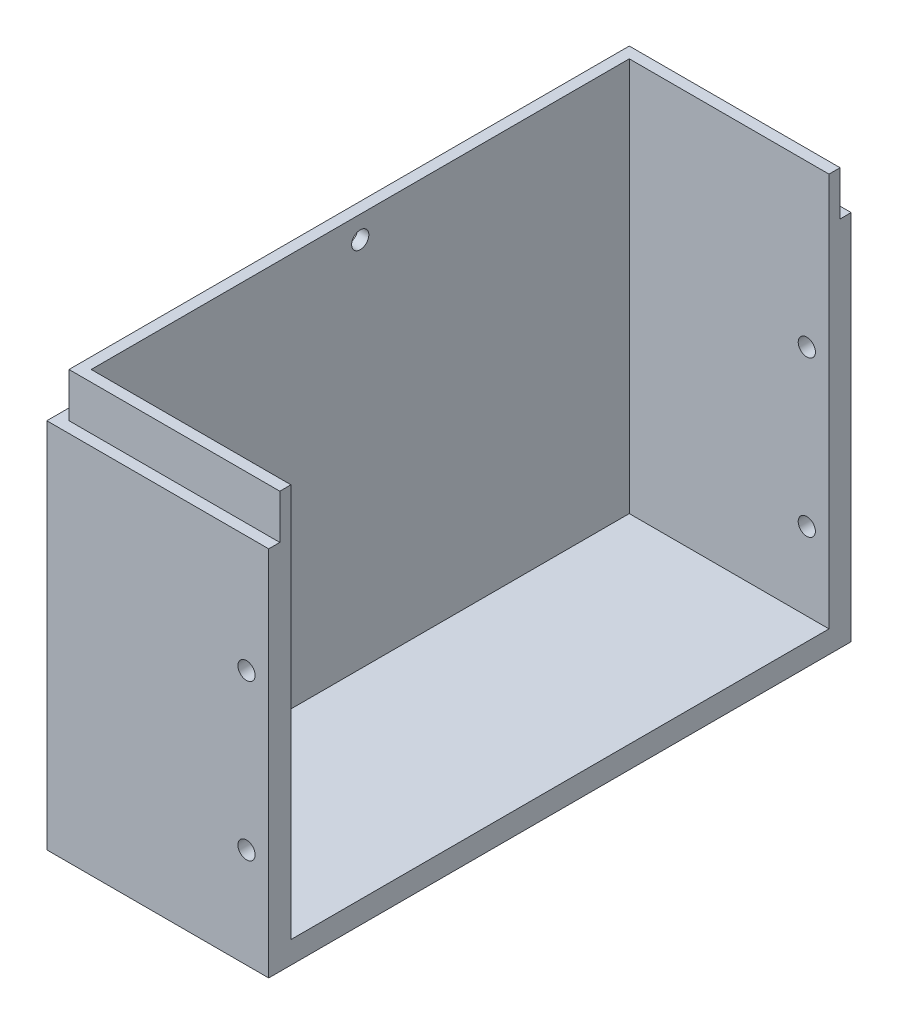
SolidWorks part; units mm, degrees
ref_plane "Front Plane" through (0, 0, 0) normal (0, 0, 1) x (1, 0, 0)
ref_plane "Top Plane" through (0, 0, 0) normal (0, 1, 0) x (1, 0, 0)
ref_plane "Right Plane" through (0, 0, 0) normal (1, 0, 0) x (0, 0, -1)
sketch "Sketch1" plane through (0, 0, 0) normal (0, 1, 0) x (1, 0, 0)
  line L1 (-20, 52.5) -> (20, 52.5)
  line L2 (-20, 52.5) -> (-20, -52.5)
  line L3 (-20, -52.5) -> (20, -52.5)
  line L4 (20, 52.5) -> (20, -52.5)
  line L5 (-20, 52.5) -> (20, -52.5) construction
  line L6 (-20, -52.5) -> (20, 52.5) construction
  point P0 (0, 0)
  dimension "D1" = 105
  dimension "D2" = 40
extrude "Boss-Extrude3" add sketch "Sketch1" along normal blind 75
sketch "Sketch4" plane through (20, 0, 0) normal (1, 0, 0) x (0, 0, -1)
  line L0 (-52.5, 75) -> (52.5, 75) construction
  line L1 (-48.5, 75) -> (48.5, 75)
  line L2 (-48.5, 75) -> (-48.5, 4)
  line L3 (-48.5, 4) -> (48.5, 4)
  line L4 (48.5, 75) -> (48.5, 4)
  line L5 (-52.5, 75) -> (-52.5, 0) construction
  line L6 (-52.5, 0) -> (52.5, 0) construction
  line L7 (52.5, 75) -> (52.5, 0) construction
  dimension "D1" = 4
  dimension "D2" = 4
  dimension "D3" = 4
extrude "Cut-Extrude2" cut sketch "Sketch4" against normal blind 36
sketch "Sketch5" plane through (0, 0, 52.5) normal (0, 0, 1) x (1, 0, 0)
  line L0 (-20, 75) -> (-20, 0) construction
  line L1 (20, 75) -> (-20, 75)
  line L2 (20, 75) -> (20, 67)
  line L3 (20, 67) -> (-20, 67)
  line L4 (-20, 75) -> (-20, 67)
  dimension "D1" = 8
extrude "Cut-Extrude3" cut sketch "Sketch5" against normal blind 2
sketch "Sketch6" plane through (0, 0, -52.5) normal (0, 0, -1) x (-1, 0, 0)
  line L0 (20, 75) -> (20, 0) construction
  line L1 (-20, 75) -> (20, 75)
  line L2 (-20, 75) -> (-20, 67)
  line L3 (-20, 67) -> (20, 67)
  line L4 (20, 75) -> (20, 67)
  dimension "D1" = 8
extrude "Cut-Extrude4" cut sketch "Sketch6" against normal blind 2
sketch "Sketch7" plane through (-20, 0, 0) normal (-1, 0, 0) x (0, 0, 1)
  line L1 (-50.5, 75) -> (50.5, 75)
  line L2 (-50.5, 75) -> (-50.5, 67)
  line L3 (-50.5, 67) -> (50.5, 67)
  line L4 (50.5, 75) -> (50.5, 67)
extrude "Cut-Extrude5" cut sketch "Sketch7" against normal blind 2
sketch "Sketch8" plane through (0, 0, 48.5) normal (0, 0, -1) x (-1, 0, 0)
  line L0 (-20, 75) -> (-20, 4) construction
  line L1 (16, 4) -> (-20, 4) construction
  circle A0 centre (-16, 18) radius 1.55
  circle A1 centre (-16, 46) radius 1.55
  dimension "D1" = 3.1
  dimension "D2" = 3.1
  dimension "D5" = 14
  dimension "D6" = 28
  dimension "D3" = 4
  dimension "D4" = 4
extrude "Cut-Extrude6" cut sketch "Sketch8" against normal through all and the other way through all
sketch "Sketch10" plane through (-18, 0, 0) normal (-1, 0, 0) x (0, 0, 1)
  line L0 (50.5, 75) -> (-50.5, 75) construction
  circle A0 centre (0, 71) radius 1.55
  dimension "D1" = 3.1
  dimension "D2" = 4
extrude "Cut-Extrude8" cut sketch "Sketch10" against normal blind 2
